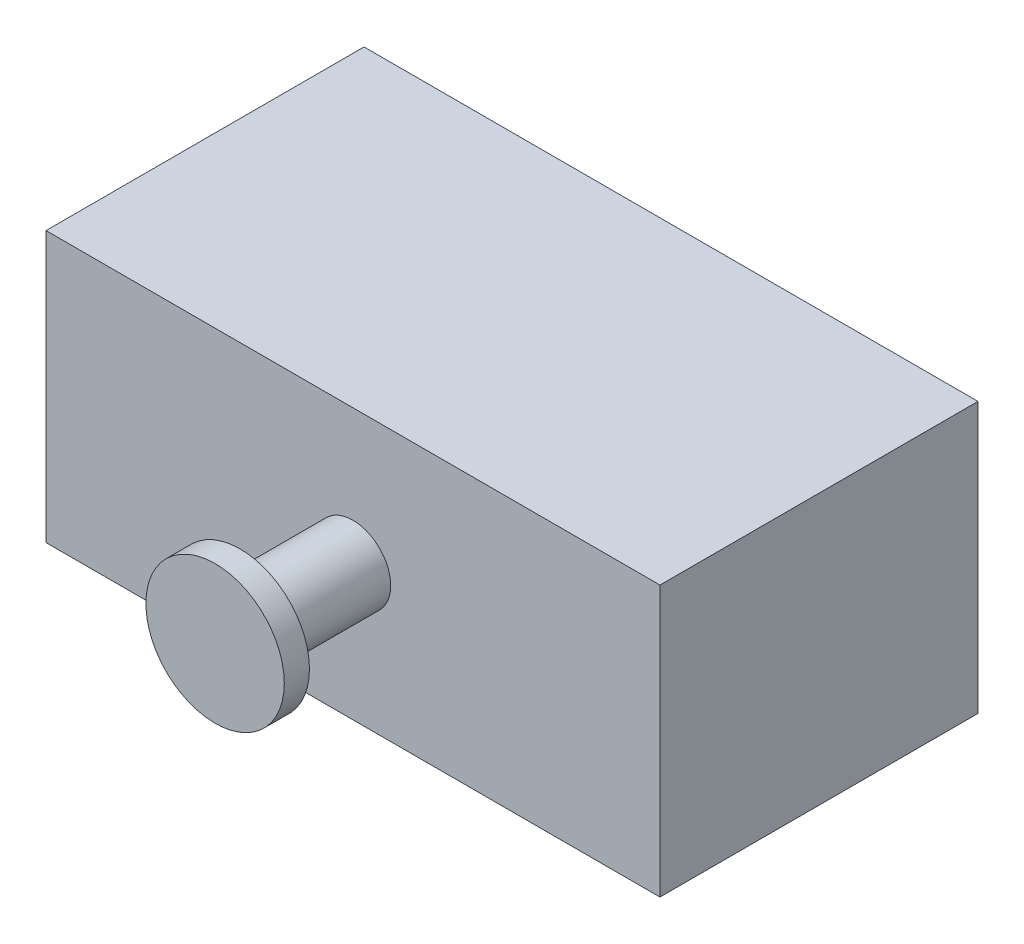
SolidWorks part; units mm, degrees
ref_plane "Front Plane" through (0, 0, 0) normal (0, 0, 1) x (1, 0, 0)
ref_plane "Top Plane" through (0, 0, 0) normal (0, 1, 0) x (1, 0, 0)
ref_plane "Right Plane" through (0, 0, 0) normal (1, 0, 0) x (0, 0, -1)
sketch "Sketch1" plane through (0, 0, 0) normal (0, 0, 1) x (1, 0, 0)
  line L1 (-43.2997, 20.7795) -> (266.5803, 20.7795)
  line L2 (-43.2997, 20.7795) -> (-43.2997, -115.6185)
  line L3 (-43.2997, -115.6185) -> (266.5803, -115.6185)
  line L4 (266.5803, 20.7795) -> (266.5803, -115.6185)
  dimension "D1" = 309.88
  dimension "D2" = 136.398
extrude "Boss-Extrude1" add sketch "Sketch1" along normal blind 160.528
sketch "Sketch2" plane through (0, 0, 160.528) normal (0, 0, 1) x (1, 0, 0)
  circle A0 centre (111.6403, -47.4195) radius 19.05
extrude "Boss-Extrude2" add sketch "Sketch2" along normal blind 56.896
sketch "Sketch3" plane through (0, 0, 217.424) normal (0, 0, 1) x (1, 0, 0)
  circle A0 centre (111.6403, -47.4195) radius 34.925
extrude "Boss-Extrude3" add sketch "Sketch3" along normal blind 12.7
